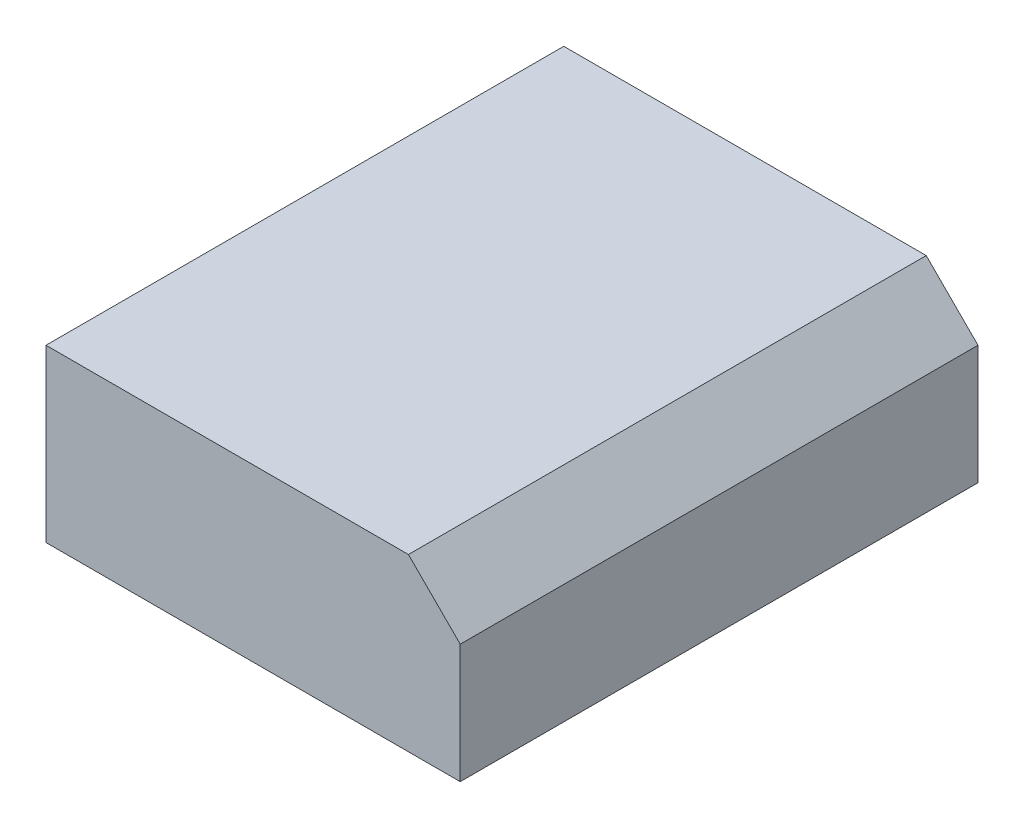
SolidWorks part; units mm, degrees
ref_plane "Спереди" through (0, 0, 0) normal (0, 0, 1) x (1, 0, 0)
ref_plane "Сверху" through (0, 0, 0) normal (0, 1, 0) x (1, 0, 0)
ref_plane "Справа" through (0, 0, 0) normal (1, 0, 0) x (0, 0, -1)
sketch "Эскиз1" plane through (0, 0, 0) normal (0, 1, 0) x (1, 0, 0)
  line L1 (-2, -2.5) -> (2, -2.5)
  line L2 (-2, -2.5) -> (-2, 2.5)
  line L3 (-2, 2.5) -> (2, 2.5)
  line L4 (2, -2.5) -> (2, 2.5)
  line L5 (-2, -2.5) -> (2, 2.5) construction
  line L6 (-2, 2.5) -> (2, -2.5) construction
  point P0 (0, 0)
  dimension "D1" = 4
  dimension "D2" = 5
extrude "Бобышка-Вытянуть1" add sketch "Эскиз1" along normal blind 1.65 from offset 0.1
chamfer "Фаска1" distance 0.5 angle 45 1 edges at (2, 1.75, 0)
sketch "Эскиз2" plane through (0, 0, 0) normal (0, 1, 0) x (1, 0, 0)
  line L1 (-1.205, -1.55) -> (1.205, -1.55)
  line L2 (-1.205, -1.55) -> (-1.205, 1.55)
  line L3 (-1.205, 1.55) -> (1.205, 1.55)
  line L4 (1.205, -1.55) -> (1.205, 1.55)
  line L5 (-1.205, -1.55) -> (1.205, 1.55) construction
  line L6 (-1.205, 1.55) -> (1.205, -1.55) construction
  point P0 (0, 0)
  dimension "D1" = 2.41
  dimension "D2" = 3.1
extrude "Бобышка-Вытянуть2" add sketch "Эскиз2" along normal blind 0.1 separate body
